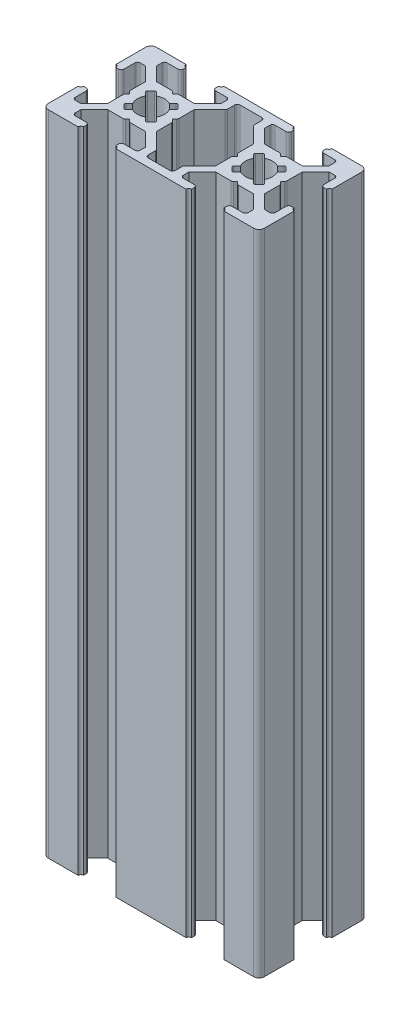
SolidWorks part; units mm, degrees
ref_plane "Front Plane" through (0, 0, 0) normal (0, 0, 1) x (1, 0, 0)
ref_plane "Top Plane" through (0, 0, 0) normal (0, 1, 0) x (1, 0, 0)
ref_plane "Right Plane" through (0, 0, 0) normal (1, 0, 0) x (0, 0, -1)
sketch "Sketch2" plane through (0, 0, 0) normal (0, 1, 0) x (1, 0, 0)
  line L0 (0, 13) -> (1.5, 13)
  line L1 (0, 0) -> (40, 0)
  line L2 (0, 0) -> (0, 20)
  line L3 (0, 20) -> (40, 20)
  line L4 (40, 0) -> (40, 20)
  line L9 (5.5, 6.5) -> (3, 4)
  line L10 (3, 4) -> (1.5, 4)
  line L11 (1.5, 4) -> (1.5, 7)
  line L12 (1.5, 7) -> (0, 7)
  line L13 (0, 7) -> (0, 13)
  line L14 (1.5, 13) -> (1.5, 16)
  line L15 (1.5, 16) -> (3, 16)
  line L16 (3, 16) -> (5.5, 13.5)
  line L17 (5.5, 10.5) -> (6, 10)
  line L18 (6, 10) -> (5.5, 9.5)
  line L19 (5.5, 9.5) -> (5.5, 10.5)
  line L20 (20, 20) -> (20, 0) construction
  line L31 (7, 18.5) -> (7, 20)
  line L32 (7, 18.5) -> (4, 18.5)
  line L33 (4, 18.5) -> (4, 17)
  line L34 (4, 17) -> (6.5, 14.5)
  line L38 (16, 18.5) -> (13, 18.5)
  line L39 (13, 18.5) -> (13, 20)
  line L40 (7, 20) -> (13, 20)
  line L41 (16, 18.5) -> (16, 17)
  line L42 (16, 17) -> (13.5, 14.5)
  line L53 (0, 10) -> (40, 10) construction
  line L89 (17.5, 18.5) -> (22.5, 18.5)
  line L90 (22.5, 18.5) -> (22.5, 16.5)
  line L91 (22.5, 16.5) -> (25.5, 13.5)
  line L92 (25.5, 13.5) -> (25.5, 6.5)
  line L93 (25.5, 6.5) -> (22.5, 3.5)
  line L94 (22.5, 3.5) -> (22.5, 1.5)
  line L95 (22.5, 1.5) -> (17.5, 1.5)
  line L96 (17.5, 1.5) -> (17.5, 3.5)
  line L97 (17.5, 3.5) -> (14.5, 6.5)
  line L98 (14.5, 6.5) -> (14.5, 13.5)
  line L99 (14.5, 13.5) -> (17.5, 16.5)
  line L100 (17.5, 16.5) -> (17.5, 18.5)
  line L102 (5.5, 13.5) -> (5.5, 10)
  line L103 (5.5, 10) -> (5.5, 6.5)
  line L104 (13.5, 14.5) -> (10, 14.5)
  line L105 (10, 14.5) -> (6.5, 14.5)
  line L106 (14.5, 10.5) -> (14.5, 9.5)
  line L107 (14.5, 9.5) -> (14, 10)
  line L108 (14, 10) -> (14.5, 10.5)
  line L109 (7, 18.5) -> (13, 18.5) construction
  line L110 (9.5, 14.5) -> (10.5, 14.5)
  line L111 (10.5, 14.5) -> (10, 14)
  line L112 (10, 14) -> (9.5, 14.5)
  line L113 (10.5, 5.5) -> (10, 6)
  line L114 (9.5, 5.5) -> (10.5, 5.5)
  line L115 (10, 6) -> (9.5, 5.5)
  line L116 (13.5, 5.5) -> (10, 5.5)
  line L117 (16, 3) -> (13.5, 5.5)
  line L118 (16, 1.5) -> (16, 3)
  line L119 (16, 1.5) -> (13, 1.5)
  line L120 (13, 1.5) -> (13, 0)
  line L121 (7, 0) -> (13, 0)
  line L122 (7, 1.5) -> (7, 0)
  line L123 (7, 1.5) -> (4, 1.5)
  line L124 (4, 1.5) -> (4, 3)
  line L125 (4, 3) -> (6.5, 5.5)
  line L126 (10, 5.5) -> (6.5, 5.5)
  line L127 (30.5, 5.5) -> (29.5, 5.5)
  line L128 (30, 6) -> (30.5, 5.5)
  line L129 (29.5, 5.5) -> (30, 6)
  line L130 (24, 3) -> (26.5, 5.5)
  line L131 (24, 1.5) -> (24, 3)
  line L132 (24, 1.5) -> (27, 1.5)
  line L133 (27, 1.5) -> (27, 0)
  line L134 (33, 0) -> (27, 0)
  line L135 (33, 1.5) -> (33, 0)
  line L136 (33, 1.5) -> (36, 1.5)
  line L137 (36, 1.5) -> (36, 3)
  line L138 (36, 3) -> (33.5, 5.5)
  line L139 (30, 5.5) -> (33.5, 5.5)
  line L140 (26.5, 5.5) -> (30, 5.5)
  line L141 (34, 10) -> (34.5, 9.5)
  line L142 (34.5, 10.5) -> (34, 10)
  line L143 (34.5, 9.5) -> (34.5, 10.5)
  line L144 (34.5, 13.5) -> (34.5, 10)
  line L145 (37, 16) -> (34.5, 13.5)
  line L146 (38.5, 16) -> (37, 16)
  line L147 (38.5, 13) -> (38.5, 16)
  line L148 (40, 13) -> (38.5, 13)
  line L149 (40, 7) -> (40, 13)
  line L150 (38.5, 7) -> (40, 7)
  line L151 (38.5, 4) -> (38.5, 7)
  line L152 (37, 4) -> (38.5, 4)
  line L153 (34.5, 6.5) -> (37, 4)
  line L154 (34.5, 10) -> (34.5, 6.5)
  line L155 (29.5, 14.5) -> (30, 14)
  line L156 (30.5, 14.5) -> (29.5, 14.5)
  line L157 (30, 14) -> (30.5, 14.5)
  line L158 (26.5, 14.5) -> (30, 14.5)
  line L159 (24, 17) -> (26.5, 14.5)
  line L160 (24, 18.5) -> (24, 17)
  line L161 (24, 18.5) -> (27, 18.5)
  line L162 (27, 18.5) -> (27, 20)
  line L163 (33, 20) -> (27, 20)
  line L164 (33, 18.5) -> (33, 20)
  line L165 (33, 18.5) -> (36, 18.5)
  line L166 (36, 18.5) -> (36, 17)
  line L167 (36, 17) -> (33.5, 14.5)
  line L168 (30, 14.5) -> (33.5, 14.5)
  line L169 (13.5, 14.5) -> (14.5, 13.5) construction
  line L170 (5.5, 6.5) -> (6.5, 5.5) construction
  line L171 (6.5, 14.5) -> (5.5, 13.5) construction
  line L172 (14.5, 6.5) -> (13.5, 5.5) construction
  line L173 (14.5, 10.5) -> (10.5, 14.5) construction
  line L174 (10.5, 5.5) -> (14.5, 9.5) construction
  line L175 (9.5, 5.5) -> (5.5, 9.5) construction
  line L176 (5.5, 10.5) -> (9.5, 14.5) construction
  line L177 (12, 13) -> (13, 12)
  line L178 (13, 12) -> (8, 7)
  line L179 (8, 7) -> (7, 8)
  line L180 (7, 8) -> (12, 13)
  line L181 (8, 13) -> (13, 8)
  line L182 (13, 8) -> (12, 7)
  line L183 (12, 7) -> (7, 12)
  line L184 (7, 12) -> (8, 13)
  line L185 (28, 7) -> (33, 12)
  line L186 (27, 8) -> (28, 7)
  line L187 (32, 13) -> (27, 8)
  line L188 (33, 12) -> (32, 13)
  line L189 (32, 7) -> (33, 8)
  line L190 (27, 12) -> (32, 7)
  line L191 (28, 13) -> (27, 12)
  line L192 (33, 8) -> (28, 13)
  line L193 (13.5, 20) -> (13, 20)
  line L194 (13, 19.5) -> (13, 20)
  line L195 (6.5, 20) -> (7, 20)
  line L196 (0, 13.5) -> (0, 13)
  line L197 (0.25, 7) -> (0, 7)
  line L198 (7, 19.5) -> (7, 20)
  line L199 (0.25, 7) -> (0, 7)
  line L200 (33, 19.5) -> (33, 20)
  line L201 (33.5, 20) -> (33, 20)
  line L202 (27, 19.5) -> (27, 20)
  line L203 (26.5, 20) -> (27, 20)
  line L204 (33, 0.5) -> (33, 0)
  line L205 (33.5, 0) -> (33, 0)
  line L206 (27, 0.5) -> (27, 0)
  line L207 (26.5, 0) -> (27, 0)
  line L208 (13, 0.5) -> (13, 0)
  line L209 (13.5, 0) -> (13, 0)
  line L210 (7, 0.5) -> (7, 0)
  line L211 (6.5, 0) -> (7, 0)
  line L212 (0.5, 13) -> (0, 13)
  line L213 (0, 6.75) -> (0, 7)
  line L214 (0, 6.75) -> (0, 7)
  line L215 (0, 7) -> (0.25, 7)
  line L216 (0, 6.5) -> (0, 7)
  line L217 (0, 7) -> (0.5, 7)
  line L218 (39.5, 13) -> (40, 13)
  line L219 (40, 13.5) -> (40, 13)
  line L220 (40, 6.5) -> (40, 7)
  line L221 (40, 7) -> (39.5, 7)
  line L222 (25.5, 9.5) -> (26, 10)
  line L223 (25.5, 10.5) -> (25.5, 9.5)
  line L224 (26, 10) -> (25.5, 10.5)
  circle A0 centre (10, 10) radius 2.5
  circle A1 centre (30, 10) radius 2.5
  arc A2 (13.5, 20) -> (13, 19.5) centre (13, 20) cw
  arc A3 (7, 19.5) -> (6.5, 20) centre (7, 20) cw
  arc A4 (0.5, 13) -> (0, 13.5) centre (0, 13) ccw
  arc A5 (0.5, 7) -> (0, 6.5) centre (0, 7) cw
  arc A6 (33, 19.5) -> (33.5, 20) centre (33, 20) ccw
  arc A7 (26.5, 20) -> (27, 19.5) centre (27, 20) ccw
  arc A8 (33, 0.5) -> (33.5, 0) centre (33, 0) cw
  arc A9 (26.5, 0) -> (27, 0.5) centre (27, 0) cw
  arc A10 (13.5, 0) -> (13, 0.5) centre (13, 0) ccw
  arc A11 (7, 0.5) -> (6.5, 0) centre (7, 0) ccw
  arc A12 (39.5, 13) -> (40, 13.5) centre (40, 13) cw
  arc A13 (39.5, 7) -> (40, 6.5) centre (40, 7) ccw
  point P19 (20, 10)
  point P103 (14.5, 10)
  dimension "D31" = 5
  dimension "D32" = 0.5
  dimension "D33" = 0.5
  dimension "D34" = 0.5
  dimension "D35" = 0.5
  dimension "D1" = 40
  dimension "D2" = 20
  dimension "D3" = 7
  dimension "D4" = 7
  dimension "D5" = 1.5
  dimension "D6" = 1.5
  dimension "D7" = 3.5
  dimension "D8" = 1.5
  dimension "D9" = 1.5
  dimension "D10" = 3
  dimension "D11" = 3
  dimension "D12" = 3.5
  dimension "D13" = 0.5
  dimension "D14" = 0.5
  dimension "D15" = 7
  dimension "D16" = 6
  dimension "D17" = 1.5
  dimension "D18" = 1.5
  dimension "D19" = 3
  dimension "D20" = 3
  dimension "D21" = 0.5
  dimension "D22" = 1.5
  dimension "D23" = 5.5
  dimension "D24" = 0.5
  dimension "D25" = 0.5
  dimension "D26" = 1.5
  dimension "D27" = 1.5
  dimension "D28" = 2
  dimension "D29" = 2
  dimension "D30" = 0.5
extrude "Boss-Extrude1" add sketch "Sketch2" along normal blind 120 contours L168 L157 L155 L158 L159 L160 L161 L162 L3 L39 L38 L41 L42 L104 L111 L112 L105 L34 L33 L32 L31 L2 L0 L14 L15 L16 L102 L17 L18 L103 L9 L10 L11 L12 L1 L122 L123 L124 L125 L126 L115 L113 L116 L117 L118 L119 L120 L133
fillet "Fillet1" radius 1 4 edges at (40, 60, -20) (40, 60, 0) (0, 60, 0) (0, 60, -20)
fillet "Fillet2" radius 0.5 6 edges at (13, 60, -18.5) (16, 60, -18.5) (10.5, 60, -14.5) (9.5, 60, -14.5) (4, 60, -18.5) (7, 60, -18.5)
fillet "Fillet3" radius 0.25 8 edges at (8, 60, -7) (7, 60, -8) (12, 60, -7) (13, 60, -8) (13, 60, -12) (12, 60, -13) (7, 60, -12) (8, 60, -13)
fillet "Fillet5" radius 0.25 8 edges at (27, 60, -8) (28, 60, -7) (32, 60, -7) (33, 60, -8) (33, 60, -12) (32, 60, -13) (27, 60, -12) (28, 60, -13)
fillet "Fillet6" radius 0.5 30 edges at (36, 60, -18.5) (33, 60, -18.5) (30.5, 60, -14.5) (29.5, 60, -14.5) (24, 60, -18.5) (27, 60, -18.5) (38.5, 60, -4) (38.5, 60, -7) (34.5, 60, -9.5) (34.5, 60, -10.5) (38.5, 60, -16) (38.5, 60, -13) (24, 60, -1.5) (27, 60, -1.5) (29.5, 60, -5.5) (30.5, 60, -5.5) (36, 60, -1.5) (33, 60, -1.5) (4, 60, -1.5) (7, 60, -1.5) (9.5, 60, -5.5) (10.5, 60, -5.5) (16, 60, -1.5) (13, 60, -1.5) (5.5, 60, -10.5) (5.5, 60, -9.5) (1.5, 60, -4) (1.5, 60, -7) (1.5, 60, -16) (1.5, 60, -13)
fillet "Fillet7" radius 0.5 8 edges at (22.5, 60, -3.5) (22.5, 60, -1.5) (17.5, 60, -3.5) (17.5, 60, -1.5) (17.5, 60, -16.5) (22.5, 60, -16.5) (22.5, 60, -18.5) (17.5, 60, -18.5)
fillet "Fillet8" radius 0.5 4 edges at (25.5, 60, -9.5) (25.5, 60, -10.5) (14.5, 60, -9.5) (14.5, 60, -10.5)
